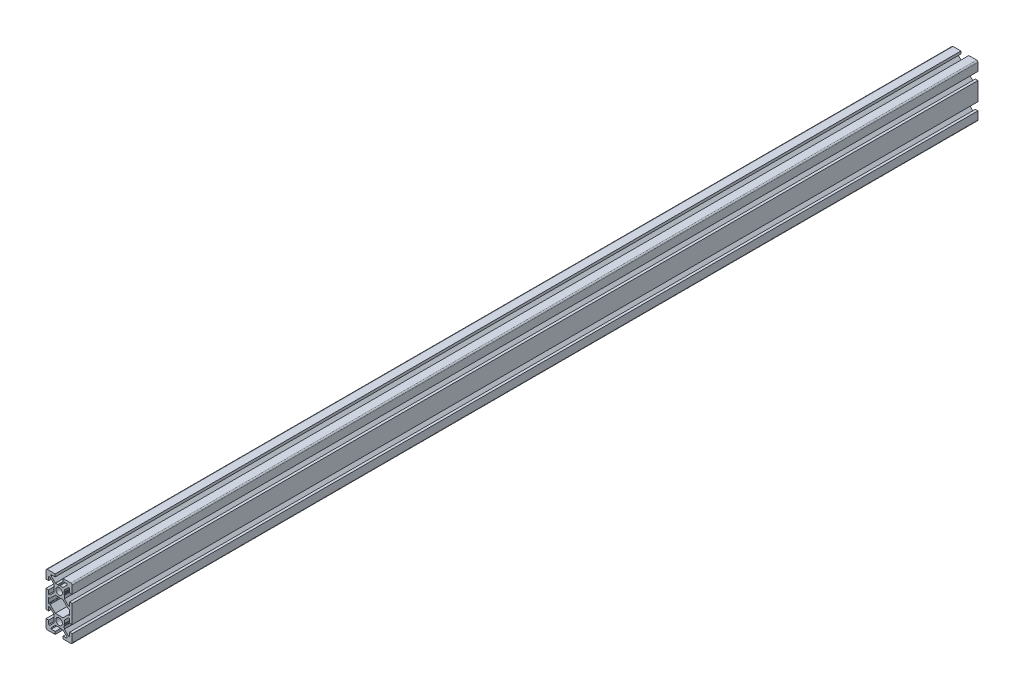
SolidWorks part; units mm, degrees
material "1060 Alloy"
ref_plane "Front Plane" through (0, 0, 0) normal (0, 0, 1) x (1, 0, 0)
ref_plane "Top Plane" through (0, 0, 0) normal (0, 1, 0) x (1, 0, 0)
ref_plane "Right Plane" through (0, 0, 0) normal (1, 0, 0) x (0, 0, -1)
ref_plane "Plane1" through (0, 0, -600) normal (0, 0, -1) x (-1, 0, 0)
sketch "Sketch1" plane through (0, 0, -600) normal (0, 0, -1) x (-1, 0, 0)
  line L0 (8, 1.7) -> (8, -1.7)
  line L1 (7.7, -2) -> (7.0636, -2)
  line L2 (6.8515, -2.0879) -> (2.9393, -6)
  line L3 (2.9393, -6) -> (-2.9393, -6)
  line L4 (-2.9393, -6) -> (-6.8515, -2.0879)
  line L5 (-7.0636, -2) -> (-7.7, -2)
  line L6 (-8, -1.7) -> (-8, 1.7)
  line L7 (-7.7, 2) -> (-7.0636, 2)
  line L8 (-6.8515, 2.0879) -> (-2.9393, 6)
  line L9 (-2.9393, 6) -> (2.9393, 6)
  line L10 (2.9393, 6) -> (6.8515, 2.0879)
  line L11 (7.0636, 2) -> (7.7, 2)
  line L12 (10, -7) -> (10, 7)
  line L13 (10, 7) -> (8, 7)
  line L14 (8, 7) -> (8, 4)
  line L15 (8, 4) -> (7.0607, 4)
  line L16 (7.0607, 4) -> (4, 7.0607)
  line L17 (4, 7.0607) -> (4, 7.5)
  line L18 (4, 7.5) -> (3.751, 8.7811)
  line L19 (3.751, 8.7811) -> (3.933, 9.0964)
  line L20 (3.933, 9.5964) -> (3.7, 10)
  line L21 (3.7, 10) -> (3.933, 10.4036)
  line L22 (4, 10.6536) -> (4, 12.9393)
  line L23 (4, 12.9393) -> (7.0607, 16)
  line L24 (7.0607, 16) -> (8, 16)
  line L25 (8, 16) -> (8, 13)
  line L26 (8, 13) -> (10, 13)
  line L27 (10, 13) -> (10, 19)
  line L28 (9, 20) -> (3, 20)
  line L29 (3, 20) -> (3, 18)
  line L30 (3, 18) -> (6, 18)
  line L31 (6, 18) -> (6, 17.0607)
  line L32 (6, 17.0607) -> (2.9393, 14)
  line L33 (2.9393, 14) -> (2.5, 14)
  line L34 (2.5, 14) -> (1.2189, 13.751)
  line L35 (1.2189, 13.751) -> (0.9036, 13.933)
  line L36 (0.4036, 13.933) -> (0, 13.7)
  line L37 (0, 13.7) -> (-0.4036, 13.933)
  line L38 (-0.6536, 14) -> (-2.9393, 14)
  line L39 (-2.9393, 14) -> (-6, 17.0607)
  line L40 (-6, 17.0607) -> (-6, 18)
  line L41 (-6, 18) -> (-3, 18)
  line L42 (-3, 18) -> (-3, 20)
  line L43 (-3, 20) -> (-9, 20)
  line L44 (-10, 19) -> (-10, 13)
  line L45 (-10, 13) -> (-8, 13)
  line L46 (-8, 13) -> (-8, 16)
  line L47 (-8, 16) -> (-7.0607, 16)
  line L48 (-7.0607, 16) -> (-4, 12.9393)
  line L49 (-4, 12.9393) -> (-4, 12.5)
  line L50 (-4, 12.5) -> (-3.751, 11.2189)
  line L51 (-3.751, 11.2189) -> (-3.933, 10.9036)
  line L52 (-3.933, 10.4036) -> (-3.7, 10)
  line L53 (-3.7, 10) -> (-3.933, 9.5964)
  line L54 (-4, 9.3464) -> (-4, 7.0607)
  line L55 (-4, 7.0607) -> (-7.0607, 4)
  line L56 (-7.0607, 4) -> (-8, 4)
  line L57 (-8, 4) -> (-8, 7)
  line L58 (-8, 7) -> (-10, 7)
  line L59 (-10, 7) -> (-10, -7)
  line L60 (-10, -7) -> (-8, -7)
  line L61 (-8, -7) -> (-8, -4)
  line L62 (-8, -4) -> (-7.0607, -4)
  line L63 (-7.0607, -4) -> (-4, -7.0607)
  line L64 (-4, -7.0607) -> (-4, -9.3464)
  line L65 (-3.933, -9.5964) -> (-3.7, -10)
  line L66 (-3.7, -10) -> (-3.933, -10.4036)
  line L67 (-3.933, -10.9036) -> (-3.751, -11.2189)
  line L68 (-3.751, -11.2189) -> (-4, -12.5)
  line L69 (-4, -12.5) -> (-4, -12.9393)
  line L70 (-4, -12.9393) -> (-7.0607, -16)
  line L71 (-7.0607, -16) -> (-8, -16)
  line L72 (-8, -16) -> (-8, -13)
  line L73 (-8, -13) -> (-10, -13)
  line L74 (-10, -13) -> (-10, -19)
  line L75 (-9, -20) -> (-3, -20)
  line L76 (-3, -20) -> (-3, -18)
  line L77 (-3, -18) -> (-6, -18)
  line L78 (-6, -18) -> (-6, -17.0607)
  line L79 (-6, -17.0607) -> (-2.9393, -14)
  line L80 (-2.9393, -14) -> (-0.6536, -14)
  line L81 (-0.4036, -13.933) -> (0, -13.7)
  line L82 (0, -13.7) -> (0.4036, -13.933)
  line L83 (0.9036, -13.933) -> (1.2189, -13.751)
  line L84 (1.2189, -13.751) -> (2.5, -14)
  line L85 (2.5, -14) -> (2.9393, -14)
  line L86 (2.9393, -14) -> (6, -17.0607)
  line L87 (6, -17.0607) -> (6, -18)
  line L88 (6, -18) -> (3, -18)
  line L89 (3, -18) -> (3, -20)
  line L90 (3, -20) -> (9, -20)
  line L91 (10, -19) -> (10, -13)
  line L92 (10, -13) -> (8, -13)
  line L93 (8, -13) -> (8, -16)
  line L94 (8, -16) -> (7.0607, -16)
  line L95 (7.0607, -16) -> (4, -12.9393)
  line L96 (4, -12.9393) -> (4, -10.6536)
  line L97 (3.933, -10.4036) -> (3.7, -10)
  line L98 (3.7, -10) -> (3.933, -9.5964)
  line L99 (3.933, -9.0964) -> (3.751, -8.7811)
  line L100 (3.751, -8.7811) -> (4, -7.5)
  line L101 (4, -7.5) -> (4, -7.0607)
  line L102 (4, -7.0607) -> (7.0607, -4)
  line L103 (7.0607, -4) -> (8, -4)
  line L104 (8, -4) -> (8, -7)
  line L105 (8, -7) -> (10, -7)
  circle A0 centre (0, -10) radius 2.5
  circle A1 centre (0, 10) radius 2.5
  arc A2 (7.7, 2) -> (8, 1.7) centre (7.7, 1.7) cw
  arc A3 (8, -1.7) -> (7.7, -2) centre (7.7, -1.7) cw
  arc A4 (7.0636, -2) -> (6.8515, -2.0879) centre (7.0636, -2.3) ccw
  arc A5 (-6.8515, -2.0879) -> (-7.0636, -2) centre (-7.0636, -2.3) ccw
  arc A6 (-7.7, -2) -> (-8, -1.7) centre (-7.7, -1.7) cw
  arc A7 (-8, 1.7) -> (-7.7, 2) centre (-7.7, 1.7) cw
  arc A8 (-7.0636, 2) -> (-6.8515, 2.0879) centre (-7.0636, 2.3) ccw
  arc A9 (6.8515, 2.0879) -> (7.0636, 2) centre (7.0636, 2.3) ccw
  arc A10 (3.933, 9.0964) -> (3.933, 9.5964) centre (3.5, 9.3464) ccw
  arc A11 (3.933, 10.4036) -> (4, 10.6536) centre (3.5, 10.6536) ccw
  arc A12 (10, 19) -> (9, 20) centre (9, 19) ccw
  arc A13 (0.9036, 13.933) -> (0.4036, 13.933) centre (0.6536, 13.5) ccw
  arc A14 (-0.4036, 13.933) -> (-0.6536, 14) centre (-0.6536, 13.5) ccw
  arc A15 (-9, 20) -> (-10, 19) centre (-9, 19) ccw
  arc A16 (-3.933, 10.9036) -> (-3.933, 10.4036) centre (-3.5, 10.6536) ccw
  arc A17 (-3.933, 9.5964) -> (-4, 9.3464) centre (-3.5, 9.3464) ccw
  arc A18 (-4, -9.3464) -> (-3.933, -9.5964) centre (-3.5, -9.3464) ccw
  arc A19 (-3.933, -10.4036) -> (-3.933, -10.9036) centre (-3.5, -10.6536) ccw
  arc A20 (-10, -19) -> (-9, -20) centre (-9, -19) ccw
  arc A21 (-0.6536, -14) -> (-0.4036, -13.933) centre (-0.6536, -13.5) ccw
  arc A22 (0.4036, -13.933) -> (0.9036, -13.933) centre (0.6536, -13.5) ccw
  arc A23 (9, -20) -> (10, -19) centre (9, -19) ccw
  arc A24 (4, -10.6536) -> (3.933, -10.4036) centre (3.5, -10.6536) ccw
  arc A25 (3.933, -9.5964) -> (3.933, -9.0964) centre (3.5, -9.3464) ccw
  dimension "D1" = 5
  dimension "D3" = 0.3
  dimension "D4" = 0.3
  dimension "D5" = 0.3
  dimension "D6" = 0.3
  dimension "D7" = 0.3
  dimension "D8" = 0.3
  dimension "D9" = 0.3
  dimension "D10" = 0.5
  dimension "D11" = 0.5
  dimension "D12" = 1
  dimension "D13" = 0.5
  dimension "D14" = 0.5
  dimension "D15" = 1
  dimension "D16" = 0.5
  dimension "D17" = 0.5
  dimension "D18" = 0.5
  dimension "D19" = 0.5
  dimension "D20" = 0.4036
  dimension "D21" = 0.5
  dimension "D22" = 0.5
  dimension "D23" = 1
  dimension "D24" = 0.5
  dimension "D25" = 0.5
  dimension "D26" = 0.4036
  dimension "D27" = 0.6536
  dimension "D28" = 0.6536
  dimension "D29" = 0.9036
  dimension "D30" = 0.9036
  dimension "D31" = 1.2189
  dimension "D32" = 1.2189
  dimension "D33" = 2.5
  dimension "D34" = 2.5
  dimension "D35" = 2.9393
  dimension "D36" = 2.9393
  dimension "D37" = 3
  dimension "D38" = 3.5
  dimension "D39" = 6
  dimension "D40" = 6.8515
  dimension "D41" = 3.7
  dimension "D42" = 3.7
  dimension "D43" = 3.751
  dimension "D44" = 3.751
  dimension "D45" = 3.933
  dimension "D46" = 3.933
  dimension "D47" = 6.8515
  dimension "D48" = 7.0607
  dimension "D49" = 7.0607
  dimension "D50" = 7.0636
  dimension "D51" = 7.0636
  dimension "D52" = 8
  dimension "D53" = 10
  dimension "D54" = 3
  dimension "D55" = 4
  dimension "D56" = 6
  dimension "D57" = 6.8515
  dimension "D58" = 6.8515
  dimension "D59" = 7.0607
  dimension "D60" = 7.0607
  dimension "D61" = 0.4036
  dimension "D62" = 0.4036
  dimension "D63" = 0.6536
  dimension "D64" = 0.6536
  dimension "D65" = 2.9393
  dimension "D66" = 2.9393
  dimension "D67" = 8
  dimension "D68" = 2
  dimension "D69" = 3.5
  dimension "D70" = 3.5
  dimension "D71" = 3.7
  dimension "D72" = 3.7
  dimension "D73" = 3.751
  dimension "D74" = 3.751
  dimension "D75" = 3.933
  dimension "D76" = 3.933
  dimension "D77" = 4
  dimension "D78" = 6
  dimension "D79" = 7
  dimension "D80" = 7.0607
  dimension "D81" = 7.0607
  dimension "D82" = 7.5
  dimension "D83" = 8.7811
  dimension "D84" = 9.0964
  dimension "D85" = 9.3464
  dimension "D86" = 9.3464
  dimension "D87" = 9.5964
  dimension "D88" = 9.5964
  dimension "D89" = 10.4036
  dimension "D90" = 12.5
  dimension "D91" = 13
  dimension "D92" = 13.5
  dimension "D93" = 13.5
  dimension "D94" = 18
  dimension "D95" = 20
  dimension "D96" = 2
  dimension "D97" = 4
  dimension "D98" = 6
  dimension "D99" = 7
  dimension "D100" = 7.0607
  dimension "D101" = 7.0607
  dimension "D102" = 7.5
  dimension "D103" = 8.7811
  dimension "D104" = 9.0964
  dimension "D105" = 9.3464
  dimension "D106" = 9.3464
  dimension "D107" = 9.5964
  dimension "D108" = 9.5964
  dimension "D109" = 10.4036
  dimension "D110" = 12.5
  dimension "D111" = 13
  dimension "D112" = 18
extrude "Boss-Extrude1" add sketch "Sketch1" against normal blind 691
sketch "Sketch2" plane through (-10, 0, 0) normal (-1, 0, 0) x (0, 0, 1)
  line L0 (91, 13) -> (91, 7) construction
  line L1 (91, 10) -> (81, 10) construction
  line L2 (91, -7) -> (91, -13) construction
  line L3 (91, -10) -> (81, -10) construction
  circle A0 centre (81, 10) radius 2
  circle A1 centre (81, -10) radius 2
  dimension "D3" = 4
  dimension "D4" = 4
  dimension "D1" = 10
  dimension "D2" = 10
extrude "Cut-Extrude1" cut sketch "Sketch2" against normal through all
ref_plane "Plane2" through (0, 0, -254.5) normal (0, 0, 1) x (1, 0, 0)
mirror "Mirror1" about plane through (0, 0, -254.5) normal (0, 0, 1) of "Cut-Extrude1"
